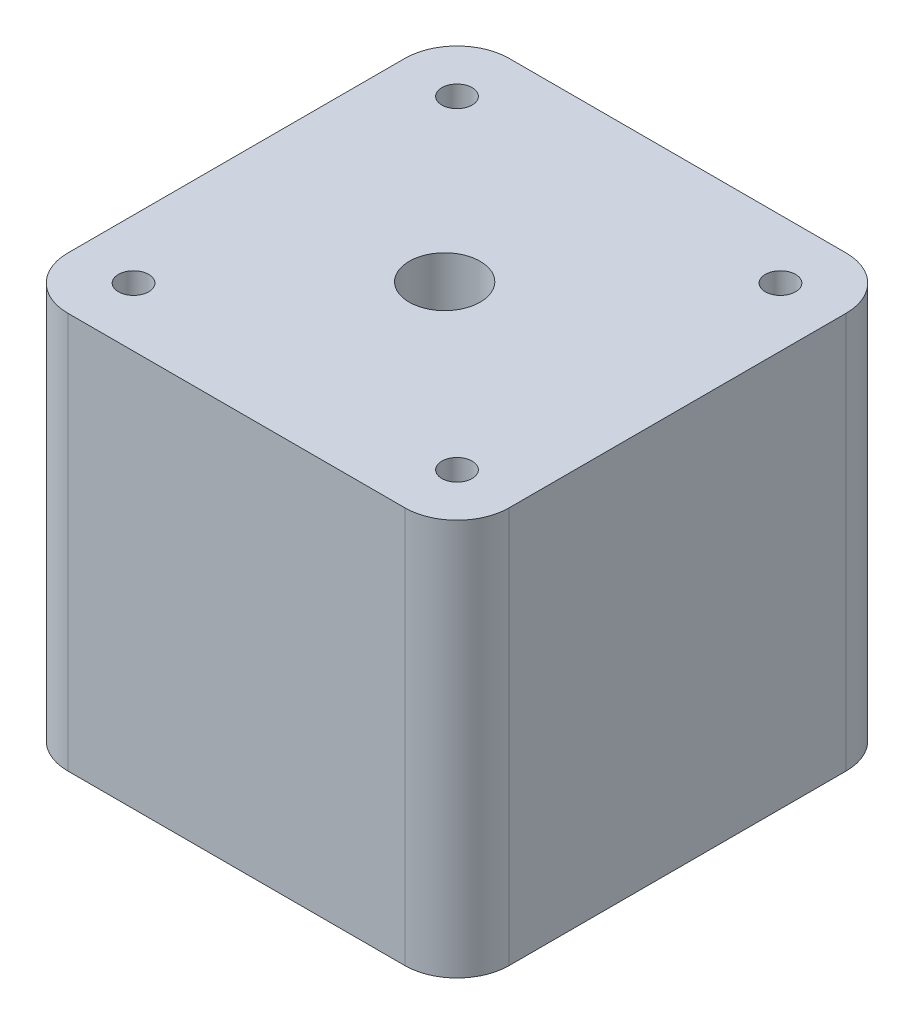
SolidWorks part; units mm, degrees
ref_plane "Front Plane" through (0, 0, 0) normal (0, 0, 1) x (1, 0, 0)
ref_plane "Top Plane" through (0, 0, 0) normal (0, 1, 0) x (1, 0, 0)
ref_plane "Right Plane" through (0, 0, 0) normal (1, 0, 0) x (0, 0, -1)
sketch "Sketch2" plane through (0, 0, 0) normal (0, 1, 0) x (1, 0, 0)
  line L1 (-22.1399, 9.9732) -> (10.1601, 9.9732)
  line L2 (-27.1399, 4.9732) -> (-27.1399, -27.3268)
  line L3 (-22.1399, -32.3268) -> (10.1601, -32.3268)
  line L4 (15.1601, 4.9732) -> (15.1601, -27.3268)
  arc A0 (-27.1399, -27.3268) -> (-22.1399, -32.3268) centre (-22.1399, -27.3268) ccw
  arc A1 (10.1601, -32.3268) -> (15.1601, -27.3268) centre (10.1601, -27.3268) ccw
  arc A2 (10.1601, 9.9732) -> (15.1601, 4.9732) centre (10.1601, 4.9732) cw
  arc A3 (-22.1399, 9.9732) -> (-27.1399, 4.9732) centre (-22.1399, 4.9732) ccw
  point P6 (-27.1399, -32.3268)
  point P11 (15.1601, 9.9732)
  point P14 (-27.1399, 9.9732)
  dimension "D3" = 5
  dimension "D1" = 42.3
  dimension "D2" = 42.3
extrude "Boss-Extrude1" add sketch "Sketch2" along normal blind 38
sketch "Sketch3" plane through (0, 38, 0) normal (0, 1, 0) x (1, 0, 0)
  line L7 (-21.4899, 4.3232) -> (9.5101, 4.3232)
  line L8 (-21.4899, 4.3232) -> (-21.4899, -26.6768)
  line L9 (-21.4899, -26.6768) -> (9.5101, -26.6768)
  line L10 (9.5101, 4.3232) -> (9.5101, -26.6768)
  dimension "D1" = 31
  dimension "D2" = 31
hole_wizard "M3.5x0.6 Tapped Hole2" positions "3DSketch2" profile "Sketch5" tap size "M3.5x0.6" standard "ANSI Metric"
sketch3d "3DSketch2"
  point P0 (-21.4899, 38, 26.6768)
  point P3 (-21.4899, 38, -4.3232)
  point P6 (9.5101, 38, -4.3232)
  point P9 (9.5101, 38, 26.6768)
sketch "Sketch5" plane through (-21.4899, 38, 26.6768) normal (1, 0, 0) x (0, 0, 1)
  line L0 (0, 0) -> (0, 5.3712)
  line L1 (0, 5.3712) -> (1.45, 4.5)
  line L2 (1.45, 4.5) -> (1.45, 0)
  line L5 (1.45, 0) -> (0, 0)
  line L10 (0, 5.3712) -> (-1.45, 4.5) construction
  line L11 (0, -6.35) -> (0, 107.95) construction
  dimension "Tap Drill Dia." = 2.9
  dimension "Tap Drill Depth" = 4.5
  dimension "Drill Angle" = 118
cosmetic thread "Hole Thread5"
cosmetic thread "Hole Thread6"
cosmetic thread "Hole Thread7"
cosmetic thread "Hole Thread8"
hole_wizard "M8 Tapped Hole1" positions "3DSketch12" profile "Sketch13" tap size "M8" standard "DIN" end condition through all
sketch3d "3DSketch12"
  point P0 (-6.6937, 38, 11.6551)
sketch "Sketch13" plane through (-6.6937, 38, 11.6551) normal (1, 0, 0) x (0, 0, 1)
  line L0 (0, 0) -> (0, 38)
  line L1 (0, 38) -> (3.4, 38)
  line L2 (3.4, 38) -> (3.4, 0)
  line L5 (3.4, 0) -> (0, 0)
  line L11 (0, -6.35) -> (0, 107.95) construction
  dimension "Thru Tap Drill Dia." = 6.8
  dimension "Thru Tap Drill Depth" = 38
cosmetic thread "Hole Thread9" parameters "D2"=8
